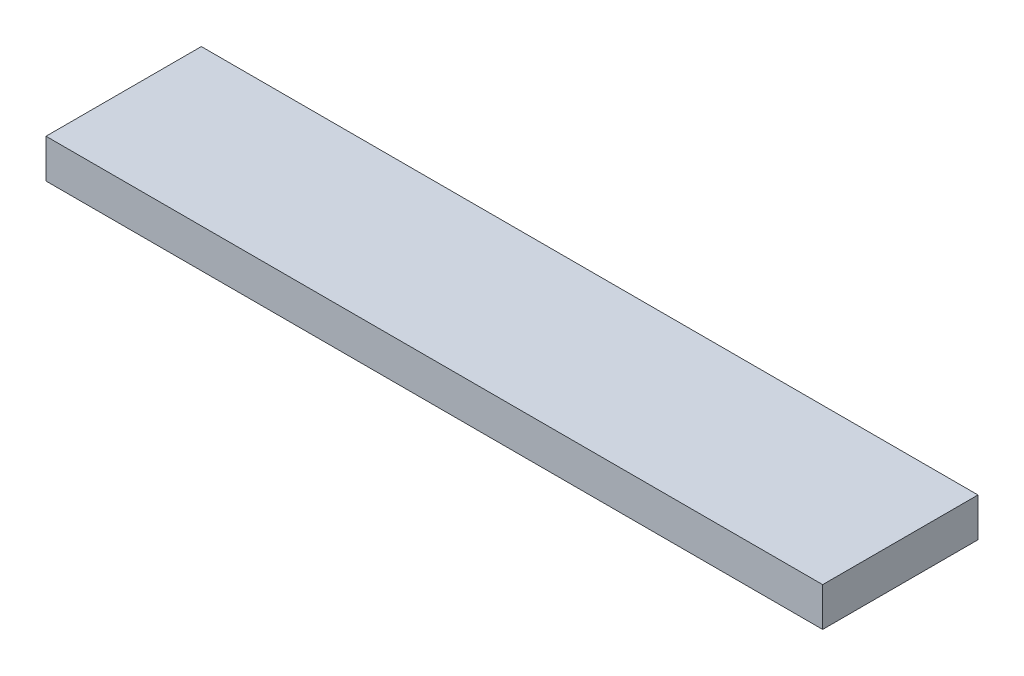
SolidWorks part; units mm, degrees
ref_plane "Front Plane" through (0, 0, 0) normal (0, 0, 1) x (1, 0, 0)
ref_plane "Top Plane" through (0, 0, 0) normal (0, 1, 0) x (1, 0, 0)
ref_plane "Right Plane" through (0, 0, 0) normal (1, 0, 0) x (0, 0, -1)
sketch "Sketch1" plane through (0, 0, 0) normal (0, 1, 0) x (1, 0, 0)
  line L1 (-63.5, 12.7) -> (63.5, 12.7)
  line L2 (-63.5, 12.7) -> (-63.5, -12.7)
  line L3 (-63.5, -12.7) -> (63.5, -12.7)
  line L4 (63.5, 12.7) -> (63.5, -12.7)
  line L5 (-63.5, 12.7) -> (63.5, -12.7) construction
  line L6 (-63.5, -12.7) -> (63.5, 12.7) construction
  point P0 (0, 0)
  dimension "D1" = 127
  dimension "D2" = 25.4
extrude "Boss-Extrude1" add sketch "Sketch1" along normal blind 6.35
